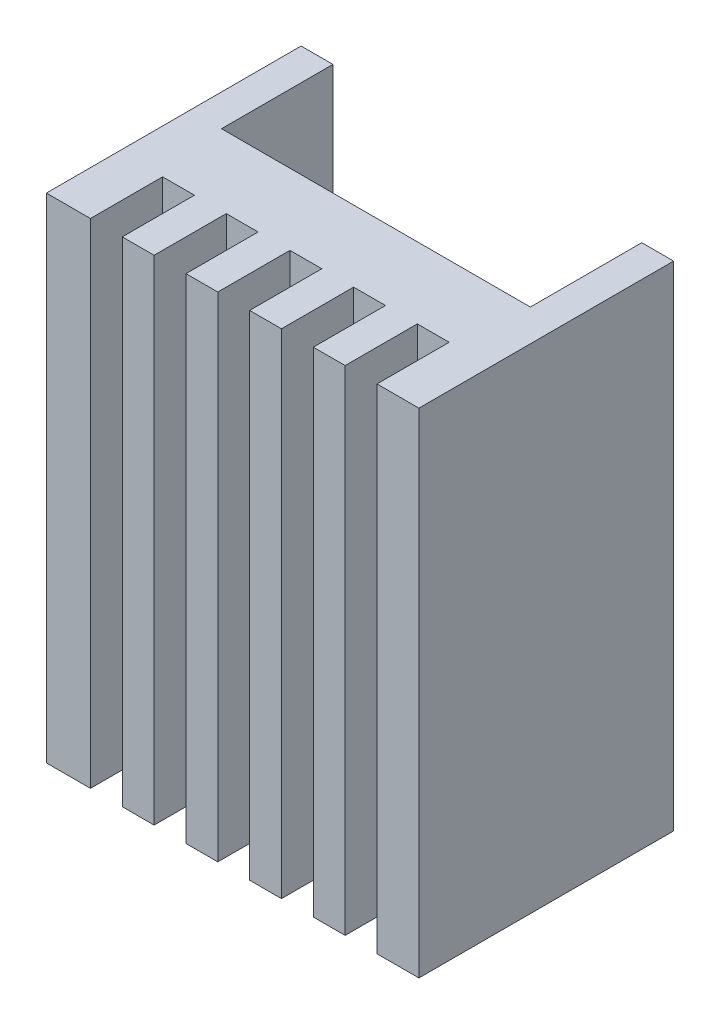
SolidWorks part; units mm, degrees
ref_plane "Front Plane" through (0, 0, 0) normal (0, 0, 1) x (1, 0, 0)
ref_plane "Top Plane" through (0, 0, 0) normal (0, 1, 0) x (1, 0, 0)
ref_plane "Right Plane" through (0, 0, 0) normal (1, 0, 0) x (0, 0, -1)
sketch "Sketch1" plane through (0, 0, 0) normal (0, 1, 0) x (1, 0, 0)
  line L0 (21.4, 16) -> (23.4, 16)
  line L1 (0, 0) -> (23.4, 0)
  line L2 (0, 0) -> (0, 16)
  line L3 (0, 16) -> (2, 16)
  line L4 (23.4, 0) -> (23.4, 16)
  line L6 (2, 16) -> (2, 9)
  line L7 (2, 9) -> (21.4, 9)
  line L8 (21.4, 16) -> (21.4, 9)
  dimension "D1" = 16
  dimension "D2" = 23.4
  dimension "D3" = 19.4
  dimension "D4" = 2
  dimension "D5" = 7
extrude "Boss-Extrude1" add sketch "Sketch1" along normal blind 31
sketch "Sketch2" plane through (0, 31, 0) normal (0, 1, 0) x (1, 0, 0)
  line L0 (0, 0) -> (23.4, 0) construction
  line L1 (2.7667, 0) -> (4.7667, 0)
  line L2 (2.7667, 0) -> (2.7667, 4.5335)
  line L3 (2.7667, 4.5335) -> (4.7667, 4.5335)
  line L4 (4.7667, 0) -> (4.7667, 4.5335)
  line L5 (6.7667, 0) -> (6.7667, 4.5335)
  line L6 (6.7667, 0) -> (8.7667, 0)
  line L7 (8.7667, 0) -> (8.7667, 4.5335)
  line L8 (6.7667, 4.5335) -> (8.7667, 4.5335)
  line L9 (10.7667, 0) -> (10.7667, 4.5335)
  line L10 (10.7667, 0) -> (12.7667, 0)
  line L11 (12.7667, 0) -> (12.7667, 4.5335)
  line L12 (10.7667, 4.5335) -> (12.7667, 4.5335)
  line L13 (14.7667, 0) -> (14.7667, 4.5335)
  line L14 (14.7667, 0) -> (16.7667, 0)
  line L15 (16.7667, 0) -> (16.7667, 4.5335)
  line L16 (14.7667, 4.5335) -> (16.7667, 4.5335)
  line L17 (18.7667, 0) -> (18.7667, 4.5335)
  line L18 (18.7667, 0) -> (20.7667, 0)
  line L19 (20.7667, 0) -> (20.7667, 4.5335)
  line L20 (18.7667, 4.5335) -> (20.7667, 4.5335)
  dimension "D2" = 2
  dimension "D1" = 5
extrude "Cut-Extrude1" cut sketch "Sketch2" against normal through all
